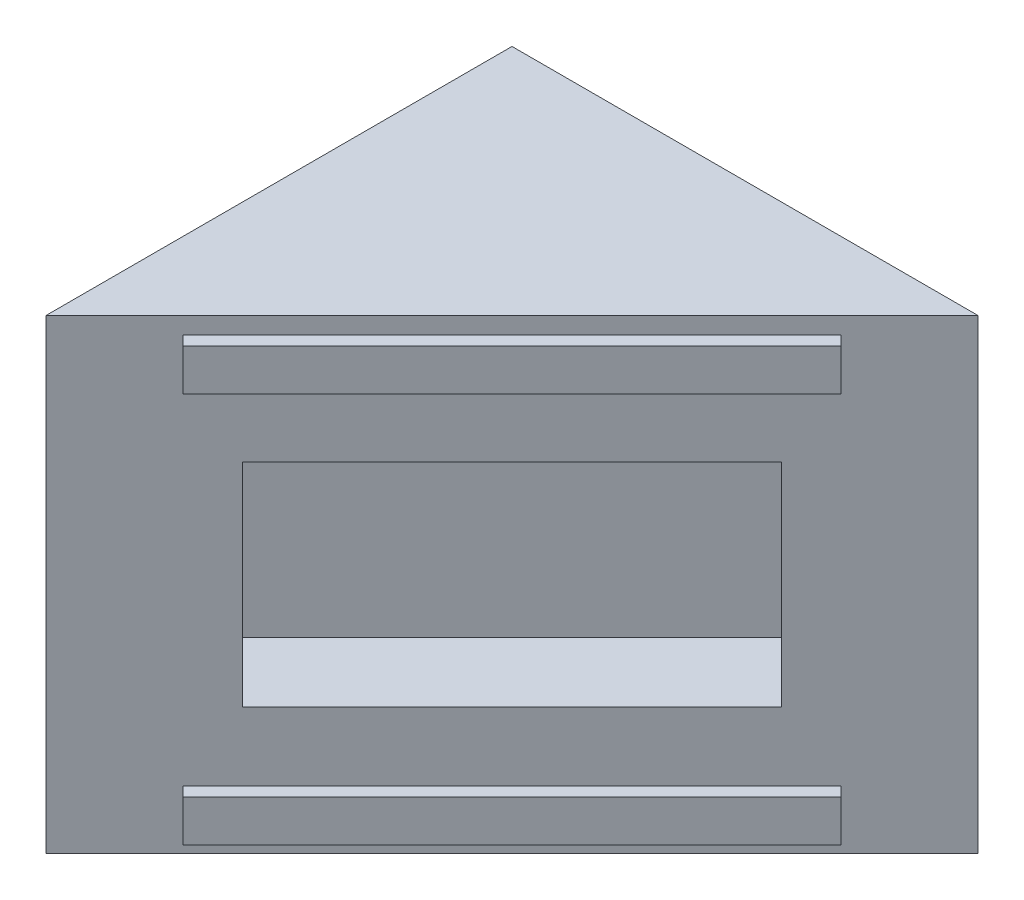
SolidWorks part; units mm, degrees
ref_plane "Front Plane" through (0, 0, 0) normal (0, 0, 1) x (1, 0, 0)
ref_plane "Top Plane" through (0, 0, 0) normal (0, 1, 0) x (1, 0, 0)
ref_plane "Right Plane" through (0, 0, 0) normal (1, 0, 0) x (0, 0, -1)
sketch "Sketch1" plane through (0, 0, 0) normal (0, 1, 0) x (1, 0, 0)
  line L1 (0, 0) -> (69.85, 0)
  line L2 (0, 0) -> (0, 69.85)
  line L3 (0, 69.85) -> (69.85, 69.85)
  line L4 (69.85, 0) -> (69.85, 69.85)
  dimension "D1" = 69.85
  dimension "D2" = 69.85
extrude "Boss-Extrude1" add sketch "Sketch1" along normal blind 69.85
ref_plane "Plane1" through (0, 0, 0) normal (0.7071, 0, 0.7071) x (0.7071, 0, -0.7071)
sketch "Sketch2" plane through (0, 0, 0) normal (0.7071, 0, 0.7071) x (0.7071, 0, -0.7071)
  line L0 (98.7828, 69.85) -> (98.7828, 0) construction
  line L1 (98.7828, 0) -> (49.3914, 0) construction
  line L2 (49.3914, 0) -> (0, 0) construction
  line L3 (0, 69.85) -> (0, 0) construction
  line L4 (49.3914, 69.85) -> (0, 69.85) construction
  line L5 (98.7828, 69.85) -> (49.3914, 69.85) construction
  line L6 (98.7828, 69.85) -> (98.7828, 0)
  line L7 (98.7828, 0) -> (49.3914, 0)
  line L8 (49.3914, 0) -> (0, 0)
  line L9 (0, 69.85) -> (0, 0)
  line L10 (49.3914, 69.85) -> (0, 69.85)
  line L11 (98.7828, 69.85) -> (49.3914, 69.85)
extrude "Cut-Extrude2" cut sketch "Sketch2" along normal blind 100
sketch "Sketch3" plane through (0, 0, 0) normal (0.7071, 0, 0.7071) x (0.7071, 0, -0.7071)
  line L0 (98.7828, 69.85) -> (0, 69.85) construction
  line L1 (14.5299, 8.763) -> (84.2529, 8.763)
  line L2 (14.5299, 67.31) -> (84.2529, 67.31)
  line L3 (0, 0) -> (98.7828, 0) construction
  line L4 (14.5299, 67.31) -> (14.5299, 61.087)
  line L5 (14.5299, 61.087) -> (84.2529, 61.087)
  line L6 (84.2529, 67.31) -> (84.2529, 61.087)
  line L7 (14.5299, 8.763) -> (14.5299, 2.54)
  line L20 (14.5299, 2.54) -> (84.2529, 2.54)
  line L21 (84.2529, 8.763) -> (84.2529, 2.54)
  point P8 (49.3914, 2.54)
  point P10 (49.3914, 61.087)
  dimension "D1" = 6.223
  dimension "D2" = 2.54
  dimension "D3" = 69.723
  dimension "D4" = 6.223
  dimension "D5" = 69.723
  dimension "D6" = 2.54
extrude "Boss-Extrude2" add sketch "Sketch3" along normal blind 2.032
sketch "Sketch4" plane through (0, 0, 0) normal (0.7071, 0, 0.7071) x (0.7071, 0, -0.7071)
  line L0 (0, 69.85) -> (98.7828, 0) construction
  line L2 (98.7828, 69.85) -> (0, 0) construction
  line L4 (20.8164, 19.05) -> (77.9664, 19.05)
  line L5 (20.8164, 19.05) -> (20.8164, 50.8)
  line L6 (20.8164, 50.8) -> (77.9664, 50.8)
  line L7 (77.9664, 19.05) -> (77.9664, 50.8)
  line L8 (20.8164, 19.05) -> (77.9664, 50.8) construction
  line L9 (20.8164, 50.8) -> (77.9664, 19.05) construction
  point P4 (49.3914, 34.925)
  dimension "D1" = 57.15
  dimension "D2" = 31.75
extrude "Cut-Extrude3" cut sketch "Sketch4" against normal blind 12.7
